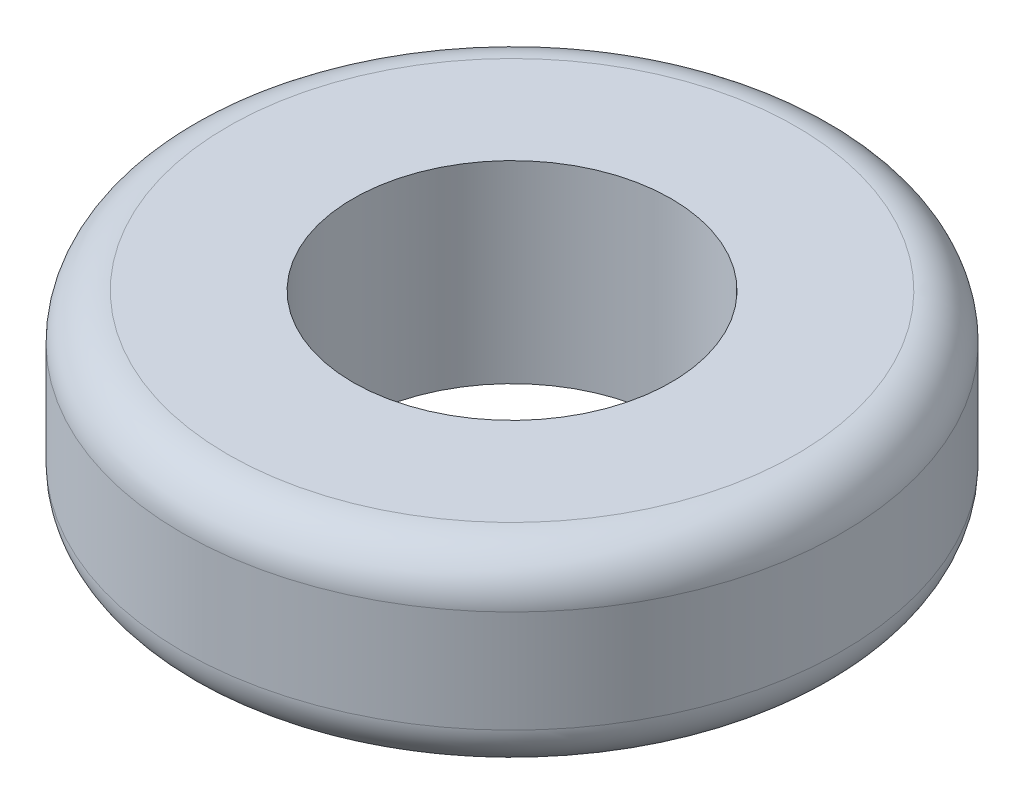
SolidWorks part; units mm, degrees
ref_plane "Front Plane" through (0, 0, 0) normal (0, 0, 1) x (1, 0, 0)
ref_plane "Top Plane" through (0, 0, 0) normal (0, 1, 0) x (1, 0, 0)
ref_plane "Right Plane" through (0, 0, 0) normal (1, 0, 0) x (0, 0, -1)
sketch "Sketch1" plane through (0, 0, 0) normal (0, 1, 0) x (1, 0, 0)
  circle A0 centre (0, 0) radius 3.5
  circle A1 centre (0, 0) radius 7.25
  dimension "D1" = 14.5
  dimension "D2" = 3.75
extrude "Boss-Extrude1" add sketch "Sketch1" along normal blind 4.25
fillet "Fillet1" radius 1 2 edges at (0, 4.25, 7.25) (0, 0, 7.25)
